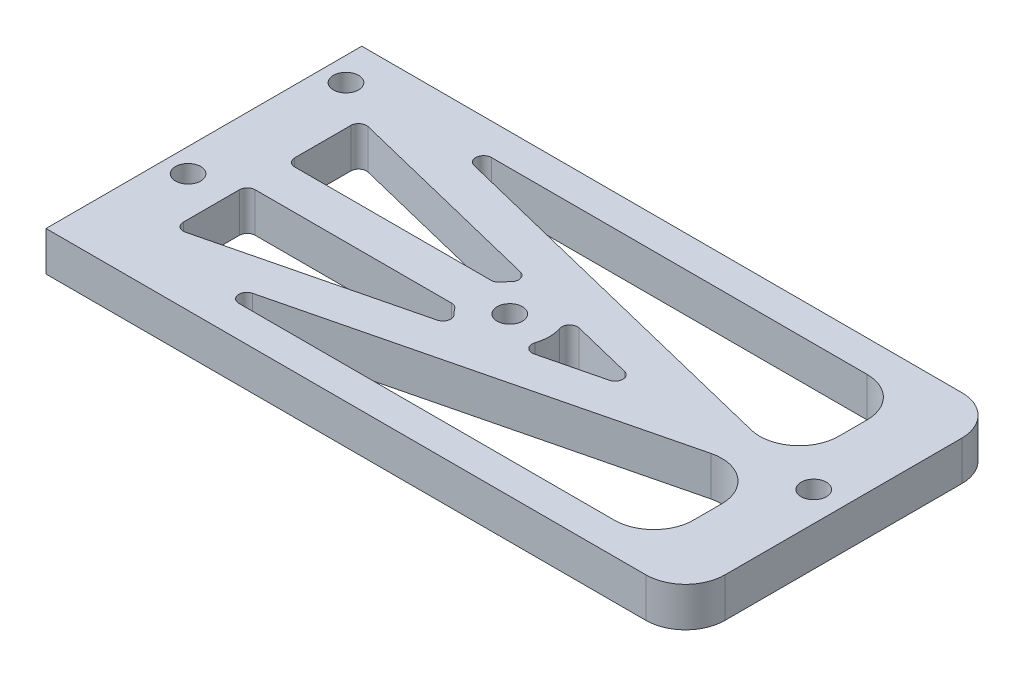
SolidWorks part; units mm, degrees
material "Thornel Mat VMA"
ref_plane "前视基准面" through (0, 0, 0) normal (0, 0, 1) x (1, 0, 0)
ref_plane "上视基准面" through (0, 0, 0) normal (0, 1, 0) x (1, 0, 0)
ref_plane "右视基准面" through (0, 0, 0) normal (1, 0, 0) x (0, 0, -1)
sketch "草图1" plane through (0, 0, 0) normal (0, 1, 0) x (1, 0, 0)
  line L1 (-40.5, 20) -> (40.5, 20)
  line L2 (-40.5, 20) -> (-40.5, -20)
  line L3 (-40.5, -20) -> (40.5, -20)
  line L4 (40.5, 20) -> (40.5, -20)
  line L5 (-40.5, 20) -> (40.5, -20) construction
  line L6 (-40.5, -20) -> (40.5, 20) construction
  point P0 (0, 0)
  dimension "D1" = 40
  dimension "D2" = 81
extrude "凸台-拉伸1" add sketch "草图1" along normal blind 5
sketch "草图2" plane through (0, 0, 0) normal (0, -1, 0) x (1, 0, 0)
  line L0 (36.75, 0) -> (-1.75, 0) construction
  line L1 (40.5, -20) -> (-40.5, -20) construction
  circle A0 centre (36.75, 0) radius 1.6
  circle A1 centre (-1.75, 0) radius 1.6
  dimension "D3" = 3.2
  dimension "D1" = 38.5
  dimension "D2" = 1.75
  dimension "D4" = 20
extrude "切除-拉伸1" cut sketch "草图2" against normal through all
fillet "圆角1" radius 5 2 edges at (40.5, 2.5, 20) (40.5, 2.5, -20)
sketch "草图3" plane through (0, 0, 0) normal (0, -1, 0) x (1, 0, 0)
  line L0 (-37.5, -15) -> (-37.5, 5) construction
  line L1 (-40.5, -20) -> (-40.5, 20) construction
  line L2 (35.5, -20) -> (-40.5, -20) construction
  circle A0 centre (-37.5, 5) radius 1.6
  circle A1 centre (-37.5, -15) radius 1.6
  dimension "D2" = 3.2
  dimension "D1" = 20
  dimension "D3" = 3
  dimension "D4" = 5
extrude "切除-拉伸2" cut sketch "草图3" against normal through all
sketch "草图4" plane through (0, 0, 0) normal (0, -1, 0) x (1, 0, 0)
  line L0 (-32.5, 16) -> (32.5, 0)
  line L1 (32.5, 0) -> (-32.5, -16)
  line L2 (-1.75, 0) -> (-35.5, 0)
  line L3 (-33.4561, 12.1159) -> (15.7649, 0)
  line L4 (-32.5, 16) -> (-32.5, -16)
  line L5 (32.5, -16) -> (32.5, 16)
  line L6 (-40.5, 20) -> (35.5, 20) construction
  line L7 (15.7649, 0) -> (-33.4561, -12.1159)
  line L8 (35.5, -15) -> (35.5, 15)
  line L9 (35.5, 15) -> (-35.5, 15)
  line L10 (-35.5, 15) -> (-35.5, -15)
  line L11 (-35.5, -15) -> (35.5, -15)
  line L12 (35.5, -16) -> (35.5, 16)
  line L13 (35.5, 16) -> (-35.5, 16)
  line L14 (-35.5, 16) -> (-35.5, -16)
  line L15 (-35.5, -16) -> (35.5, -16)
  line L16 (35.5, -20) -> (-40.5, -20) construction
  line L17 (-1.75, 2.5) -> (-35.5, 2.5)
  line L18 (-1.75, -2.5) -> (-35.5, -2.5)
  line L19 (-32.261, 16.971) -> (36.6838, 0)
  line L20 (36.6838, 0) -> (-32.261, -16.971)
  circle A2 centre (-1.75, 0) radius 5
  dimension "D5" = 10
  dimension "D3" = 4
  dimension "D4" = 4
  dimension "D1" = 5
  dimension "D2" = 3
  dimension "D6" = 4
  dimension "D7" = 2.5
  dimension "D8" = 2.5
  dimension "D9" = 1
extrude "切除-拉伸5" cut sketch "草图4" against normal blind 10 contours A2 L3 L4 L17 | A2 L18 L4 L7 | A2 L7 L3 | L13 L19 L5 | L5 L20 L15
fillet "圆角2" radius 5 2 edges at (32.5, 2.5, 1.0299) (32.5, 2.5, -1.0299)
fillet "圆角3" radius 5 2 edges at (32.5, 2.5, 16) (32.5, 2.5, -16)
fillet "圆角4" radius 1 3 edges at (15.7649, 2.5, 0) (1.9053, 2.5, 3.4116) (1.9053, 2.5, -3.4116)
fillet "圆角5" radius 1 10 edges at (-32.5, 2.5, -11.8806) (-32.5, 2.5, -2.5) (-6.0801, 2.5, -2.5) (-3.404, 2.5, -4.7185) (-32.5, 2.5, 2.5) (-3.404, 2.5, 4.7185) (-6.0801, 2.5, 2.5) (-28.3162, 2.5, -16) (-28.3162, 2.5, 16) (-32.5, 2.5, 11.8806)
